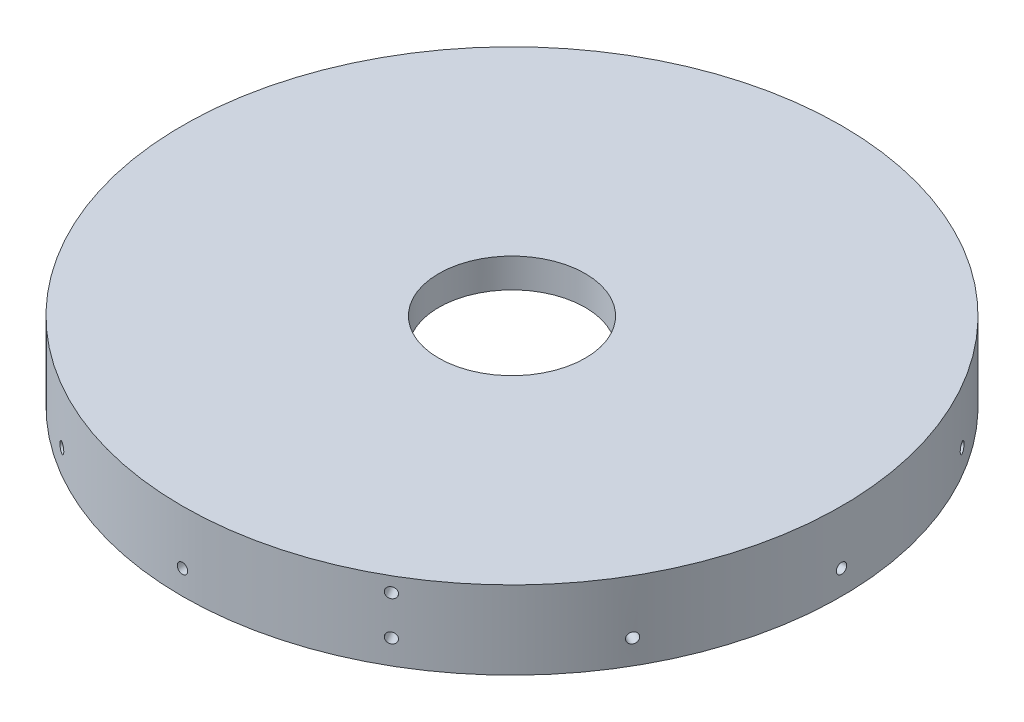
SolidWorks part; units mm, degrees
material "6061-T6 (SS)"
ref_plane "Front Plane" through (0, 0, 0) normal (0, 0, 1) x (1, 0, 0)
ref_plane "Top Plane" through (0, 0, 0) normal (0, 1, 0) x (1, 0, 0)
ref_plane "Right Plane" through (0, 0, 0) normal (1, 0, 0) x (0, 0, -1)
sketch "Sketch1" plane through (0, 0, 0) normal (0, 1, 0) x (1, 0, 0)
  circle A0 centre (0, 0) radius 85.6615
  dimension "D1" = 171.323
extrude "Boss-Extrude1" add sketch "Sketch1" along normal mid plane 7.62
sketch "Sketch2" plane through (0, -3.81, 0) normal (0, -1, 0) x (1, 0, 0)
  circle A0 centre (0, 0) radius 19.05
  dimension "D1" = 38.1
extrude "Cut-Extrude1" cut sketch "Sketch2" against normal up to surface (7.62 mm away) up to face at (0, 3.81, 85.6615)
sketch "Sketch4" plane through (0, -3.81, 0) normal (0, -1, 0) x (1, 0, 0)
  circle A0 centre (0, 0) radius 85.6615
  circle A1 centre (0, 0) radius 79.375
  dimension "D1" = 171.323
  dimension "D2" = 158.75
extrude "Boss-Extrude2" add sketch "Sketch4" along normal blind 12.7
ref_plane "Plane1" through (-85.6615, 0, 0) normal (-1, 0, 0) x (0, 0, 1)
sketch "Sketch3" plane through (-85.6615, 0, 0) normal (-1, 0, 0) x (0, 0, 1)
  circle A0 centre (0, 0) radius 1.3525
  dimension "D1" = 2.7051
extrude "Cut-Extrude2" cut sketch "Sketch3" against normal blind 15.24
pattern_circular "CirPattern1" count 3 over 360 about axis through (0, 0, 0) along (0, 1, 0) of "Cut-Extrude2"
sketch "Sketch5" plane through (-85.6615, 0, 0) normal (-1, 0, 0) x (0, 0, 1)
  line L0 (0, -4.191) -> (0, 4.191) construction
  line L1 (-79.375, -16.51) -> (79.375, -16.51) construction
  circle A0 centre (0, -10.1828) radius 1.3525
  dimension "D1" = 2.7051
  dimension "D2" = 6.3272
extrude "Cut-Extrude3" cut sketch "Sketch5" against normal blind 17.018
pattern_circular "CirPattern2" count 12 over 360 about axis through (0, 3.81, 0) along (0, -1, 0) of "Cut-Extrude3"
